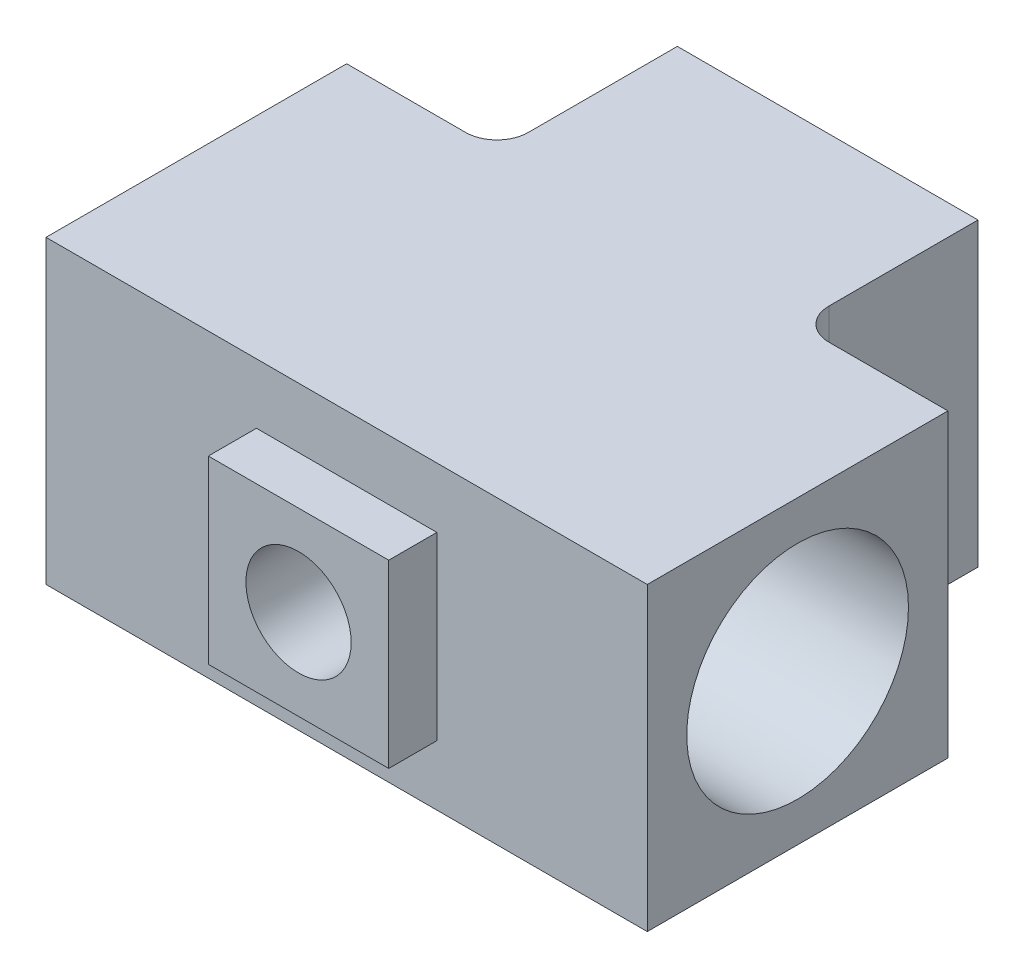
SolidWorks part; units mm, degrees
material "6061 Alloy"
ref_plane "X-Y Datum" through (0, 0, 0) normal (0, 0, 1) x (1, 0, 0)
ref_plane "X-Z Datum" through (0, 0, 0) normal (0, 1, 0) x (1, 0, 0)
ref_plane "Y-Z Datum" through (0, 0, 0) normal (1, 0, 0) x (0, 0, -1)
sketch "Sketch2" plane through (0, 0, 0) normal (0, 1, 0) x (1, 0, 0)
  line L0 (0, 15.875) -> (0, 34.925) construction
  line L1 (-31.75, -15.875) -> (31.75, -15.875)
  line L2 (-31.75, -15.875) -> (-31.75, 15.875)
  line L3 (-31.75, 15.875) -> (31.75, 15.875)
  line L4 (31.75, -15.875) -> (31.75, 15.875)
  line L5 (-31.75, -15.875) -> (31.75, 15.875) construction
  line L6 (-31.75, 15.875) -> (31.75, -15.875) construction
  line L7 (15.875, 15.875) -> (15.875, 34.925)
  line L8 (-15.875, 15.875) -> (-15.875, 34.925)
  line L9 (-15.875, 34.925) -> (15.875, 34.925)
  point P0 (0, 0)
  dimension "D1" = 31.75
  dimension "D2" = 63.5
  dimension "D5" = 19.05
  dimension "D3" = 31.75
extrude "Boss-Extrude1" add sketch "Sketch2" along normal blind 31.75 contours L1 L4 L3 L2 | L9 L8 L3 L7
hole_wizard "59/64 (0.92188) Diameter Hole1" positions "Sketch7" profile "Sketch6" hole size "59/64" standard "ANSI Inch" end condition through all
sketch "Sketch7" plane through (31.75, 0, 0) normal (1, 0, 0) x (0, 0, -1)
  line L0 (-15.875, 31.75) -> (15.875, 0)
  point P0 (0, 15.875)
sketch "Sketch6" plane through (31.75, 15.875, 0) normal (0, 1, 0) x (0, 0, -1)
  line L0 (0, 0) -> (0, 63.5)
  line L1 (0, 63.5) -> (11.7079, 63.5)
  line L2 (11.7079, 63.5) -> (11.7079, 0)
  line L5 (11.7079, 0) -> (0, 0)
  line L11 (0, -6.35) -> (0, 107.95) construction
  dimension "Thru Hole Dia." = 23.4158
  dimension "Thru Hole Depth" = 63.5
hole_wizard "59/64 (0.92188) Diameter Hole2" positions "Sketch8" profile "Sketch9" hole size "59/64" standard "ANSI Inch"
sketch "Sketch8" plane through (0, 0, -34.925) normal (0, 0, -1) x (-1, 0, 0)
  line L0 (-15.875, 31.75) -> (15.875, 0)
  point P0 (0, 15.875)
  point P10 (0, 12.7)
sketch "Sketch9" plane through (0, 15.875, -34.925) normal (1, 0, 0) x (0, 1, 0)
  line L0 (0, 0) -> (0, 41.3248)
  line L1 (0, 41.3248) -> (11.7079, 34.29)
  line L2 (11.7079, 34.29) -> (11.7079, 0)
  line L5 (11.7079, 0) -> (0, 0)
  line L10 (0, 41.3248) -> (-11.7079, 34.29) construction
  line L11 (0, -6.35) -> (0, 107.95) construction
  dimension "Hole Dia." = 23.4158
  dimension "Hole Depth" = 34.29
  dimension "Drill Angle" = 118
sketch "Sketch10" plane through (0, 0, 15.875) normal (0, 0, 1) x (1, 0, 0)
  line L0 (-31.75, 31.75) -> (31.75, 0)
  line L2 (-9.525, 6.35) -> (9.525, 6.35)
  line L3 (-9.525, 6.35) -> (-9.525, 25.4)
  line L4 (-9.525, 25.4) -> (9.525, 25.4)
  line L5 (9.525, 6.35) -> (9.525, 25.4)
  line L6 (-9.525, 6.35) -> (9.525, 25.4) construction
  line L7 (-9.525, 25.4) -> (9.525, 6.35) construction
  point P4 (0, 15.875)
  dimension "D1" = 19.05
  dimension "D2" = 19.05
extrude "Boss-Extrude2" add sketch "Sketch10" along normal blind 5.08 contours L2 L5 L0 L3 | L0 L5 L4 L3
hole_wizard "7/16 (0.4375) Diameter Hole1" positions "Sketch11" profile "Sketch12" hole size "7/16" standard "ANSI Inch"
sketch "Sketch11" plane through (0, 0, 20.955) normal (0, 0, 1) x (1, 0, 0)
  line L0 (-9.525, 25.4) -> (9.525, 6.35)
  point P0 (0, 15.875)
  point P9 (0, 12.7)
sketch "Sketch12" plane through (0, 15.875, 20.955) normal (1, 0, 0) x (0, -1, 0)
  line L0 (0, 0) -> (0, 28.7385)
  line L1 (0, 28.7385) -> (5.5562, 25.4)
  line L2 (5.5562, 25.4) -> (5.5562, 0)
  line L5 (5.5562, 0) -> (0, 0)
  line L10 (0, 28.7385) -> (-5.5563, 25.4) construction
  line L11 (0, -6.35) -> (0, 107.95) construction
  dimension "Hole Dia." = 11.1125
  dimension "Hole Depth" = 25.4
  dimension "Drill Angle" = 118
fillet "Fillet1" radius 3.302 2 edges at (15.875, 15.875, -15.875) (-15.875, 15.875, -15.875)
thread "Thread1" pitch 1.8143 start angle 0, offset 0, length 0, pitch 1.8143, diameter 23.4158
ref_plane "Plane1" through (31.75, 15.875, 11.7079) normal (0, -1, 0) x (0, 0, 1)
sketch "Thread Profile1" plane through (31.75, 15.875, 11.7079) normal (0, -1, 0) x (0, 0, 1)
  line L0 (0, 0) -> (0, 1.8143) construction
  line L1 (0, 0) -> (0.982, 0.567)
  line L2 (0.982, 0.567) -> (0.982, 0.7937)
  line L3 (0.982, 0.7937) -> (0, 1.3607)
  line L4 (0.982, 0.6804) -> (0, 0.6804) construction
  line L11 (0, 0) -> (0, 1.3607)
  point P2 (0, 0)
  dimension "Pitch" = 1.8143
  dimension "Profile_Angle" = 60
  dimension "Profile_Land" = 0.2268
  dimension "Profile_Height" = 0.982
thread "Thread2" pitch 1.8143 start angle 0, offset 0, length 0, pitch 1.8143, diameter 23.4158
ref_plane "Plane2" through (-31.75, 15.875, -11.7079) normal (0, -1, 0) x (0, 0, -1)
sketch "Thread Profile2" plane through (-31.75, 15.875, -11.7079) normal (0, -1, 0) x (0, 0, -1)
  line L0 (0, 0) -> (0, 1.8143) construction
  line L1 (0, 0) -> (0.982, 0.567)
  line L2 (0.982, 0.567) -> (0.982, 0.7937)
  line L3 (0.982, 0.7937) -> (0, 1.3607)
  line L4 (0.982, 0.6804) -> (0, 0.6804) construction
  line L11 (0, 0) -> (0, 1.3607)
  point P2 (0, 0)
  dimension "Pitch" = 1.8143
  dimension "Profile_Angle" = 60
  dimension "Profile_Land" = 0.2268
  dimension "Profile_Height" = 0.982
thread "Thread3" pitch 1.8143 start angle 0, offset 0, length 0, pitch 1.8143, diameter 23.4158
ref_plane "Plane3" through (11.7079, 15.875, -34.925) normal (0, -1, 0) x (1, 0, 0)
sketch "Thread Profile3" plane through (11.7079, 15.875, -34.925) normal (0, -1, 0) x (1, 0, 0)
  line L0 (0, 0) -> (0, 1.8143) construction
  line L1 (0, 0) -> (0.982, 0.567)
  line L2 (0.982, 0.567) -> (0.982, 0.7937)
  line L3 (0.982, 0.7937) -> (0, 1.3607)
  line L4 (0.982, 0.6804) -> (0, 0.6804) construction
  line L11 (0, 0) -> (0, 1.3607)
  point P2 (0, 0)
  dimension "Pitch" = 1.8143
  dimension "Profile_Angle" = 60
  dimension "Profile_Land" = 0.2268
  dimension "Profile_Height" = 0.982
thread "Thread4" pitch 1.8143 start angle 0, offset 0, length 0, pitch 1.8143, diameter 11.1125
ref_plane "Plane4" through (-5.5562, 15.875, 23.495) normal (0, -1, 0) x (-1, 0, 0)
sketch "Thread Profile4" plane through (-5.5562, 15.875, 23.495) normal (0, -1, 0) x (-1, 0, 0)
  line L0 (0, 0) -> (0, 1.8143) construction
  line L1 (0, 0) -> (0.982, 0.567)
  line L2 (0.982, 0.567) -> (0.982, 0.7937)
  line L3 (0.982, 0.7937) -> (0, 1.3607)
  line L4 (0.982, 0.6804) -> (0, 0.6804) construction
  line L11 (0, 0) -> (0, 1.3607)
  point P2 (0, 0)
  dimension "Pitch" = 1.8143
  dimension "Profile_Angle" = 60
  dimension "Profile_Land" = 0.2268
  dimension "Profile_Height" = 0.982
